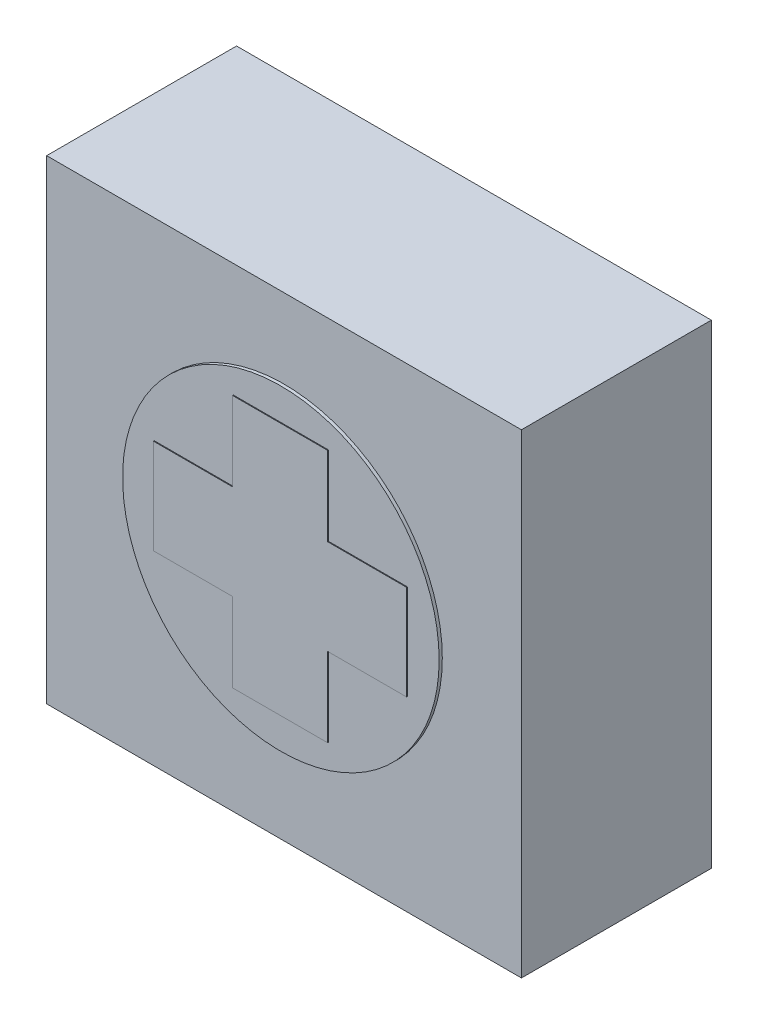
SolidWorks part; units mm, degrees
ref_plane "Front Plane" through (0, 0, 0) normal (0, 0, 1) x (1, 0, 0)
ref_plane "Top Plane" through (0, 0, 0) normal (0, 1, 0) x (1, 0, 0)
ref_plane "Right Plane" through (0, 0, 0) normal (1, 0, 0) x (0, 0, -1)
sketch "Sketch1" plane through (0, 0, 0) normal (0, 0, 1) x (1, 0, 0)
  line L1 (-75, 75) -> (75, 75)
  line L2 (-75, 75) -> (-75, -75)
  line L3 (-75, -75) -> (75, -75)
  line L4 (75, 75) -> (75, -75)
  line L5 (-75, 75) -> (75, -75) construction
  line L6 (-75, -75) -> (75, 75) construction
  point P0 (0, 0)
  dimension "D1" = 150
extrude "Boss-Extrude1" add sketch "Sketch1" along normal mid plane 60
sketch "Sketch2" plane through (0, 0, 30) normal (0, 0, 1) x (1, 0, 0)
  circle A0 centre (0, 0) radius 50
  dimension "D1" = 100
extrude "Boss-Extrude2" add sketch "Sketch2" along normal blind 1
sketch "Sketch3" plane through (0, 0, 30) normal (0, 0, 1) x (1, 0, 0)
  line L1 (-15, 40) -> (15, 40)
  line L2 (-15, 40) -> (-15, -40)
  line L3 (-15, -40) -> (15, -40)
  line L4 (15, 40) -> (15, -40)
  line L5 (-15, 40) -> (15, -40) construction
  line L6 (-15, -40) -> (15, 40) construction
  line L7 (-40, -15) -> (40, -15)
  line L8 (-40, -15) -> (-40, 15)
  line L9 (-40, 15) -> (40, 15)
  line L10 (40, -15) -> (40, 15)
  line L11 (-40, -15) -> (40, 15) construction
  line L12 (-40, 15) -> (40, -15) construction
  point P0 (0, 0)
  point P8 (0, 0)
  dimension "D1" = 30
  dimension "D2" = 30
  dimension "D3" = 80
  dimension "D4" = 80
extrude "Boss-Extrude3" add sketch "Sketch3" along normal blind 1.25 contours L9 L8 L7 L2 | L9 L2 L7 L4 | L2 L9 L4 L1 | L7 L10 L9 L4 | L7 L2 L3 L4
scale "Scale1" scale about centroid uniform scaling yes scale factor 0.5
sketch "Sketch4" plane through (0, 0, 15.7243) normal (0, 0, 1) x (1, 0, 0)
  point P0 (0, 0)
